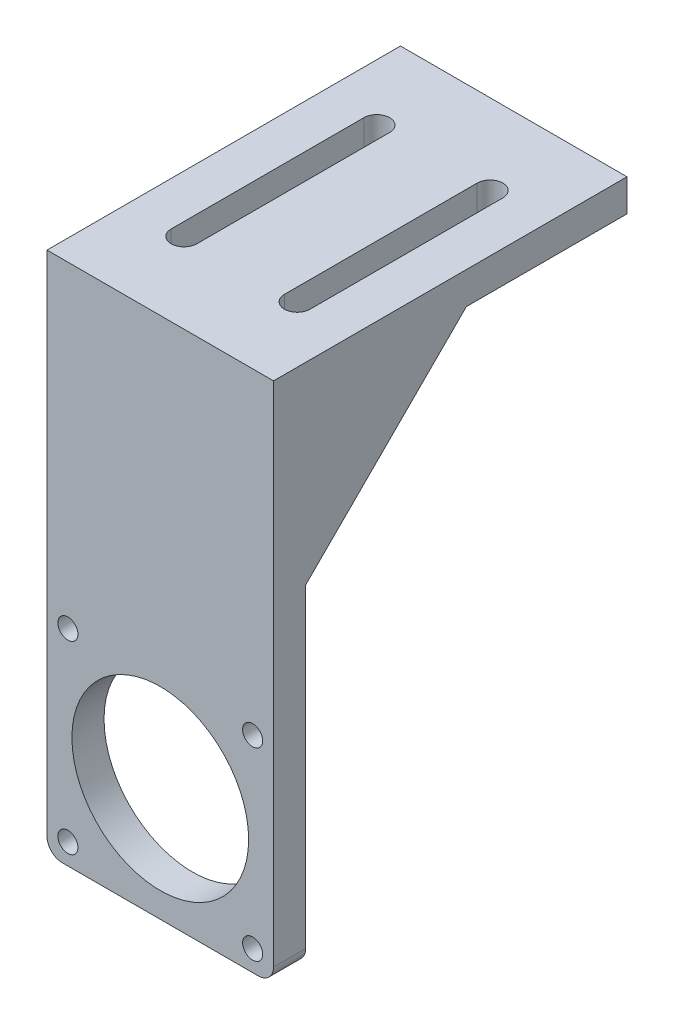
SolidWorks part; units mm, degrees
ref_plane "前视基准面" through (0, 0, 0) normal (0, 0, 1) x (1, 0, 0)
ref_plane "上视基准面" through (0, 0, 0) normal (0, 1, 0) x (1, 0, 0)
ref_plane "右视基准面" through (0, 0, 0) normal (1, 0, 0) x (0, 0, -1)
sketch "草图1" plane through (0, 0, 0) normal (0, 0, 1) x (1, 0, 0)
  line L0 (0.3493, -2.1329) -> (-46.6195, -2.1329) construction
  line L1 (0.3493, -2.1329) -> (46.6195, -2.1329) construction
  line L2 (0.3493, -2.1329) -> (0.3493, -46.7194) construction
  line L3 (14.4493, -14.3328) -> (14.4493, 44.8671)
  line L4 (0.3493, -16.2329) -> (12.5491, -16.2329)
  line L5 (-13.7507, 44.8671) -> (-13.7507, -14.3328)
  line L7 (0.3493, -16.2329) -> (-11.8506, -16.2329)
  line L8 (14.4493, 44.8671) -> (-13.7507, 44.8671)
  circle A0 centre (-11.1507, 9.3671) radius 1.25
  circle A1 centre (11.8493, 9.3671) radius 1.25
  circle A2 centre (-11.1507, -13.6329) radius 1.25
  circle A3 centre (11.8493, -13.6329) radius 1.25
  arc A4 (-11.8506, -16.2329) -> (-13.7507, -14.3328) centre (-11.8506, -14.3328) cw
  arc A5 (12.5491, -16.2329) -> (14.4493, -14.3328) centre (12.5491, -14.3328) ccw
  circle A8 centre (0.3493, -2.1329) radius 11
  point P9 (14.4493, -2.1329)
  point P10 (-13.7507, -2.1329)
  point P11 (0.3493, 11.9671)
  point P12 (0.3493, -16.2329)
  dimension "D1" = 1.9002
extrude "凸台-拉伸1" add sketch "草图1" along normal blind 4
ref_plane "基准面1" through (0, 44.8671, 0) normal (0, 1, 0) x (1, 0, 0)
sketch "草图2" plane through (0, 44.8671, 0) normal (0, 1, 0) x (1, 0, 0)
  line L0 (-13.7507, 0) -> (-13.7507, -4)
  line L1 (0.3493, -4) -> (0.3493, 40) construction
  line L2 (14.4493, 0) -> (14.4493, -4)
  line L3 (14.4493, -4) -> (-13.7507, -4)
  line L4 (-13.7507, 0) -> (-13.7507, 40)
  line L5 (-13.7507, 40) -> (14.4493, 40)
  line L6 (14.4493, 40) -> (14.4493, 0)
  line L7 (0.3493, 18) -> (14.4493, 18) construction
  line L8 (0.3493, 18) -> (-13.7507, 18) construction
  line L9 (5.7993, 6) -> (5.7993, 30)
  line L10 (8.9993, 6) -> (8.9993, 30)
  line L11 (-8.3007, 6) -> (-8.3007, 30)
  line L12 (-5.1007, 6) -> (-5.1007, 30)
  arc A0 (8.9993, 6) -> (5.7993, 6) centre (7.3993, 6) cw
  arc A1 (8.9993, 30) -> (5.7993, 30) centre (7.3993, 30) ccw
  arc A2 (8.9993, 6) -> (5.7993, 6) centre (7.3993, 6) cw
  arc A3 (8.9993, 30) -> (5.7993, 30) centre (7.3993, 30) ccw
  arc A4 (-8.3007, 30) -> (-5.1007, 30) centre (-6.7007, 30) cw
  arc A5 (-8.3007, 6) -> (-5.1007, 6) centre (-6.7007, 6) ccw
  arc A6 (-8.3007, 30) -> (-5.1007, 30) centre (-6.7007, 30) cw
  arc A7 (-8.3007, 6) -> (-5.1007, 6) centre (-6.7007, 6) ccw
  point P15 (5.7993, 18)
  point P19 (8.9993, 18)
  point P25 (-8.3007, 18)
  point P26 (-5.1007, 18)
extrude "凸台-拉伸2" add sketch "草图2" along normal blind 4
ref_plane "基准面2" through (14.4493, 0, 0) normal (1, 0, 0) x (0, 0, -1)
sketch "草图3" plane through (14.4493, 0, 0) normal (1, 0, 0) x (0, 0, -1)
  line L0 (20, 44.8671) -> (0, 44.8671)
  line L1 (0, 44.8671) -> (0, 24.8671)
  line L2 (0, 24.8671) -> (20, 44.8671)
extrude "凸台-拉伸3" add sketch "草图3" against normal blind 2
ref_plane "基准面3" through (0.3493, 0, 0) normal (1, 0, 0) x (0, 0, -1)
mirror "镜向2" about plane through (0.3493, 0, 0) normal (1, 0, 0) of "凸台-拉伸3"
